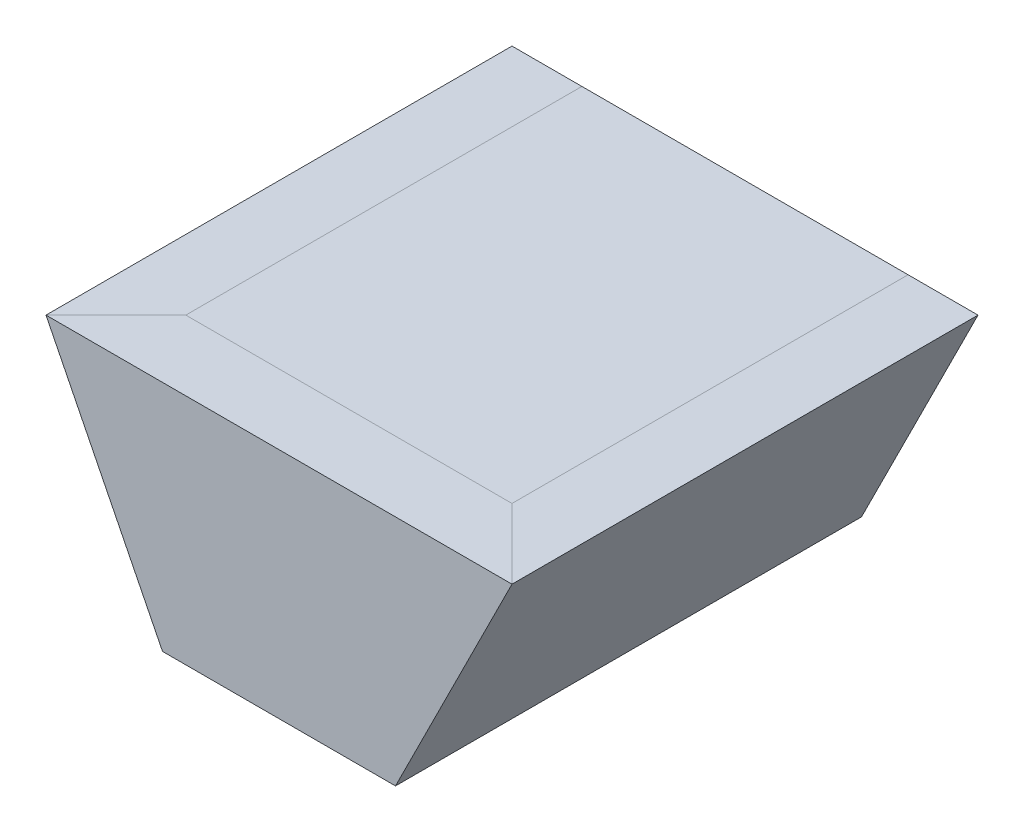
SolidWorks part; units mm, degrees
ref_plane "Ebene vorne" through (0, 0, 0) normal (0, 0, 1) x (1, 0, 0)
ref_plane "Ebene oben" through (0, 0, 0) normal (0, 1, 0) x (1, 0, 0)
ref_plane "Ebene rechts" through (0, 0, 0) normal (1, 0, 0) x (0, 0, -1)
sketch "Skizze1" plane through (0, 0, 0) normal (0, 0, 1) x (1, 0, 0)
  line L0 (0, 0) -> (50, -100)
  line L1 (50, -100) -> (150, -100)
  line L2 (150, -100) -> (200, 0)
  line L3 (200, 0) -> (0, 0)
  point P5 (1.0704, 0)
  dimension "D1" = 200
  dimension "D2" = 100
  dimension "D3" = 100
extrude "Aufsatz-Linear austragen1" add sketch "Skizze1" against normal blind 200
sketch "Skizze2" plane through (0, 0, 0) normal (0, 1, 0) x (1, 0, 0)
  line L4 (30, 30) -> (0, 0)
  line L5 (170, 30) -> (200, 0)
  line L6 (200, 200) -> (0, 200) construction
  line L8 (30, 30) -> (170, 30)
  line L9 (170, 30) -> (170, 170)
  line L10 (170, 170) -> (30, 170)
  line L11 (30, 170) -> (30, 30)
  line L13 (170, 30) -> (170, 200)
  line L15 (30, 200) -> (30, 30)
  dimension "D1" = 30
split line "Trennlinie8"
sketch "Skizze3" plane through (0, 0, -200) normal (0, 0, -1) x (-1, 0, 0)
  line L0 (-170, 0) -> (-130, -80)
  line L1 (-50, -100) -> (-150, -100) construction
  line L2 (-30, 0) -> (-70, -80)
  line L3 (0, 0) -> (-50, -100) construction
  line L4 (-150, -100) -> (-200, 0) construction
  line L5 (-130, -80) -> (-70, -80)
  dimension "D1" = 20
split line "Trennlinie9"
sketch "Skizze8" plane through (0, 0, 0) normal (0, 1, 0) x (1, 0, 0)
  line L0 (170, 30) -> (30, 30)
split line "Trennlinie10"
sketch "Skizze9" plane through (0, 0, -200) normal (0, 0, -1) x (-1, 0, 0)
  line L0 (-130, -80) -> (-150, -100)
  line L1 (-70, -80) -> (-50, -100)
split line "Trennlinie11"
